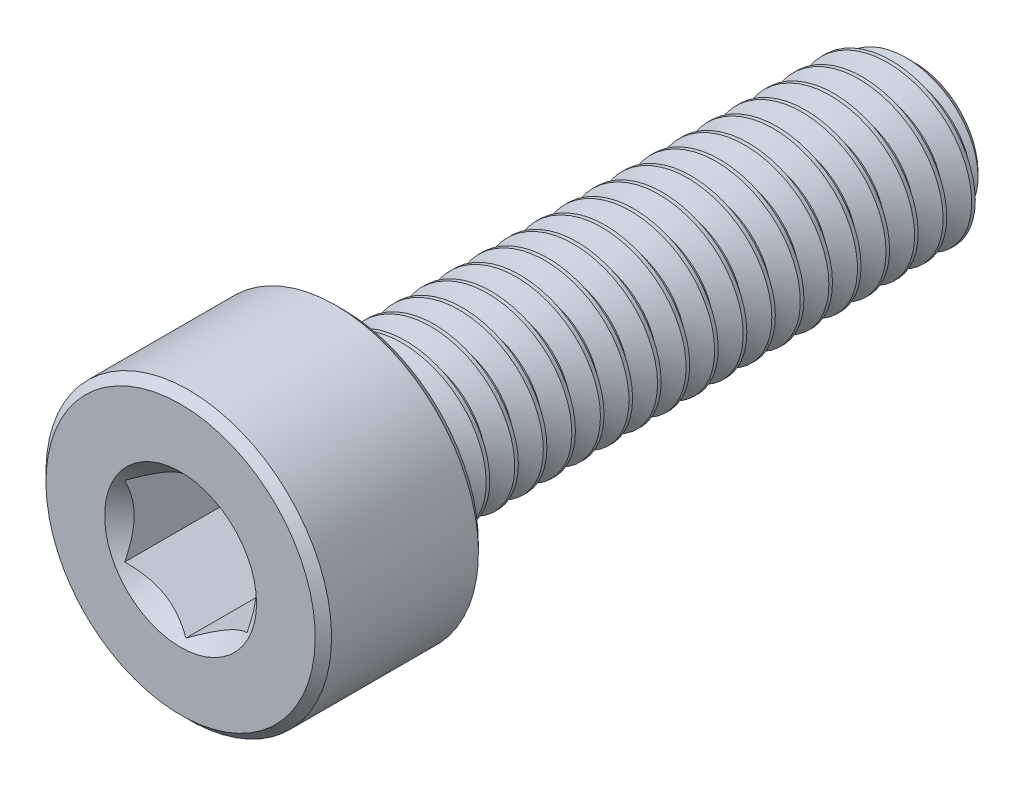
SolidWorks part; units mm, degrees
ref_plane "Front Plane" through (0, 0, 0) normal (0, 0, 1) x (1, 0, 0)
ref_plane "Top Plane" through (0, 0, 0) normal (0, 1, 0) x (1, 0, 0)
ref_plane "Right Plane" through (0, 0, 0) normal (1, 0, 0) x (0, 0, -1)
sketch "Sketch1" plane through (0, 0, 0) normal (1, 0, 0) x (0, 0, -1)
  line L0 (-9, 0) -> (9, 0) construction
  line L1 (9, 0) -> (9, 1.5453) construction
  line L2 (9, 1.5453) -> (8.5453, 2) construction
  line L3 (8.5453, 2) -> (8.475, 2) construction
  line L4 (8.475, 2) -> (-5, 2) construction
  line L5 (-5, 2) -> (-5, 3.5) construction
  line L6 (-5, 3.5) -> (-9, 3.5) construction
  line L7 (-9, 3.5) -> (-9, 0) construction
  line L8 (9, 1.5453) -> (9, 2) construction
  line L9 (8.9563, 2.0758) -> (9.3063, 1.4696) construction
  line L10 (9.3063, 1.4696) -> (9.6563, 2.0758) construction
  line L11 (9.6563, 2.0758) -> (8.9563, 2.0758) construction
  line L12 (9.3063, 2.0758) -> (9.3063, 2) construction
  line L13 (9.3063, 1.4696) -> (9.3063, 1.5453) construction
  line L14 (9.2625, 1.5453) -> (9.35, 1.5453) construction
  line L15 (9, 2) -> (9.6125, 2) construction
  line L16 (8.9781, 2.0379) -> (9.6344, 2.0379) construction
  line L17 (9, 0) -> (9, -2) construction
  line L18 (-5.2, 3.5) -> (-5, 3.3) construction
  line L19 (-8.8, 3.5) -> (-9, 3.3) construction
  line L20 (-5, 2) -> (-5, 0) construction
  line L21 (-5, 1) -> (-0.3333, 1) construction
  line L22 (-0.3333, 1) -> (4.3333, 1) construction
  line L23 (4.3333, 1) -> (9, 1) construction
  line L24 (-0.3333, 1) -> (-0.3333, 2) construction
  line L25 (-0.3333, 2) -> (-0.3333, 3.5) construction
  line L26 (4.3333, 1) -> (4.3333, 3.5) construction
  point P0 (-9, 1.5)
  point P3 (7.25, 2)
  point P4 (0, 0)
  point P18 (4.3333, 2)
  point P22 (9.3063, 1.5453)
  point P24 (8.475, 2)
  point P25 (9.3063, 2)
  point P28 (9.3063, 2.0379)
  point P29 (7.25, -2)
  point P30 (-0.3333, 2)
  point P31 (-7, 3.5)
  point P37 (-5.7, 3.5)
  point P38 (-8.7, 3.5)
  point P45 (-0.3333, 1)
  point P46 (4.3333, 1)
  dimension "D2" = 0.0875
  dimension "D7" = 0.2
  dimension "D8" = 0.2
  dimension "D9" = 0.2
  dimension "D10" = 0.1
  dimension "D11" = 0.5
  dimension "Drive Size" = 3
  dimension "Head Diameter" = 7
  dimension "Head Height" = 4
  dimension "Thread Pitch" = 0.7
  dimension "Thread Size" = 4
  dimension "Length" = 14
  dimension "D12" = 0.525
  dimension "D4" = 1.75
  dimension "D3" = 45
sketch "Sketch2" plane through (0, 0, 0) normal (1, 0, 0) x (0, 0, -1)
  line L0 (-9, 0) -> (-9, 3.3)
  line L1 (-8.8, 3.5) -> (-5.2, 3.5)
  line L2 (-5, 3.3) -> (-5, 2.2)
  line L4 (8.5453, 2) -> (9, 1.5453)
  line L5 (9, 1.5453) -> (9, 0)
  line L6 (-5, 3.5) -> (-9, 3.5) construction
  line L7 (9, 0) -> (-9, 0)
  line L8 (-8.8, 3.5) -> (-9, 3.3) construction
  line L10 (-8.8, 3.5) -> (-9, 3.3)
  line L14 (-5.2, 3.5) -> (-5, 3.3) construction
  line L16 (-5.2, 3.5) -> (-5, 3.3)
  line L17 (-5, 2) -> (-5, 3.5) construction
  line L19 (-4.8, 2) -> (8.5453, 2)
  line L20 (8.475, 2) -> (-5, 2) construction
  arc A1 (-5, 2.2) -> (-4.8, 2) centre (-4.8, 2.2) ccw
  dimension "D3" = 0.2
revolve "Revolve1" add sketch "Sketch2" angle 360 about L7
sketch "Sketch3" plane through (0, 0, 9) normal (0, 0, 1) x (1, 0, 0)
  line L1 (1.5, -0.866) -> (1.5, 0.866)
  line L2 (1.5, 0.866) -> (0, 1.7321)
  line L3 (0, 1.7321) -> (-1.5, 0.866)
  line L4 (-1.5, 0.866) -> (-1.5, -0.866)
  line L5 (-1.5, -0.866) -> (0, -1.7321)
  line L6 (0, -1.7321) -> (1.5, -0.866)
  circle A0 centre (0, 0) radius 1.5 construction
  circle A1 centre (0, 0) radius 3.5 construction
  circle A2 centre (0, 0) radius 3.5 construction
  circle A3 centre (0, 0) radius 1.7321 construction
  point P13 (0, 0)
  dimension "D1" = 3.4641
extrude "Cut-Extrude1" cut sketch "Sketch3" against normal offset from surface (3 mm away) 1 up to face at (0, 3.3, 5)
sketch "Sketch4" plane through (0, 0, 9) normal (0, 0, 1) x (1, 0, 0)
  circle A0 centre (0, 0) radius 1.862
  dimension "D1" = 3.7239
extrude "Cut-Extrude2" cut sketch "Sketch4" against normal up to vertex (2 mm away) draft 45 up to point (0, 3.5, 7)
sketch "Sketch11" plane through (0, 0, 0) normal (1, 0, 0) x (0, 0, -1)
  line L0 (-9, 0) -> (9, 0) construction
  line L1 (-9, 0) -> (9, 0) construction
  line L2 (-2.375, 0) -> (-2.375, 2) construction
  line L3 (8.475, 2) -> (-5, 2) construction
  line L4 (6.375, 0) -> (6.375, 2) construction
  line L6 (9, 1.5453) -> (9, 2) construction
  point P2 (-2.375, 0)
  point P3 (6.375, 0)
  dimension "D1" = 2.625
  dimension "D2" = 2.625
sketch "Sketch6" plane through (0, 0, -9) normal (0, 0, -1) x (-1, 0, 0)
  circle A0 centre (0, 0) radius 2
curve "Helix/Spiral1" pitch 0.7 height 14.7 turns 21
sketch "Sketch10" plane through (0, 0, 0) normal (1, 0, 0) x (0, 0, -1)
  line L0 (-4.8, -3.5) -> (-4.8, 3.5)
  line L5 (-9, 0) -> (9, 0) construction
  line L6 (-4.8, 2) -> (-4.8, -2) construction
  point P3 (-4.8, 0)
split "Split1" trim tools "Sketch10" bodies to split 106 resulting bodies 114 115
sketch "Sketch7" plane through (0, 0, 0) normal (1, 0, 0) x (0, 0, -1)
  line L0 (8.9781, 2.0379) -> (9.6344, 2.0379)
  line L1 (9.6344, 2.0379) -> (9.35, 1.5453)
  line L2 (9.35, 1.5453) -> (9.2625, 1.5453)
  line L3 (9.2625, 1.5453) -> (8.9781, 2.0379)
sweep "Cut-Sweep1" cut profiles "Sketch7" path "Helix/Spiral1"
sketch "Sketch8" plane through (0, 0, 0) normal (1, 0, 0) x (0, 0, -1)
  line L0 (-5, 0) -> (-5, 2)
  line L1 (-4.8, -2) -> (-4.8, 2) construction
  line L2 (-5, 2) -> (-4.8, 2)
  line L4 (-4.8, 2) -> (-3.6453, 0)
  line L5 (-3.6453, 0) -> (-5, 0)
  line L6 (8.475, 2) -> (-5, 2) construction
  line L7 (-9, 0) -> (9, 0) construction
  dimension "D1" = 60
revolve "Revolve2" add sketch "Sketch8" angle 360 about L5
equation "\"D2@Sketch1\" = \"Thread Pitch@Sketch1\" / 8"
equation "\"D4@Helix/Spiral1\" = \"Thread Pitch@Sketch1\""
equation "\"D7@Sketch1\" = \"Head Height@Sketch1\" * .05"
equation "\"D8@Sketch1\"=\"D7@Sketch1\""
equation "\"D9@Sketch1\"=\"D7@Sketch1\""
equation "\"D10@Sketch1\"=\"D7@Sketch1\"/2"
equation "\"D11@Sketch1\"=\"D10@Sketch1\"*5"
equation "\"D4@Sketch1\"=\"Thread Pitch@Sketch1\"*2.5"
equation "\"D12@Sketch1\"=\"Thread Pitch@Sketch1\"*.75"
equation "\"D3@Helix/Spiral1\"=\"Length@Sketch1\"+\"Thread Pitch@Sketch1\""
equation "\"D3@Sketch2\"=\"Thread Size@Sketch1\"*0.05"
equation "\"D1@Sketch11\"=\"Length@Sketch1\"*0.1875"
equation "\"D2@Sketch11\"=\"D1@Sketch11\""
equation "\"D1@Sketch4\"=\"D1@Sketch3\"*1.075"
